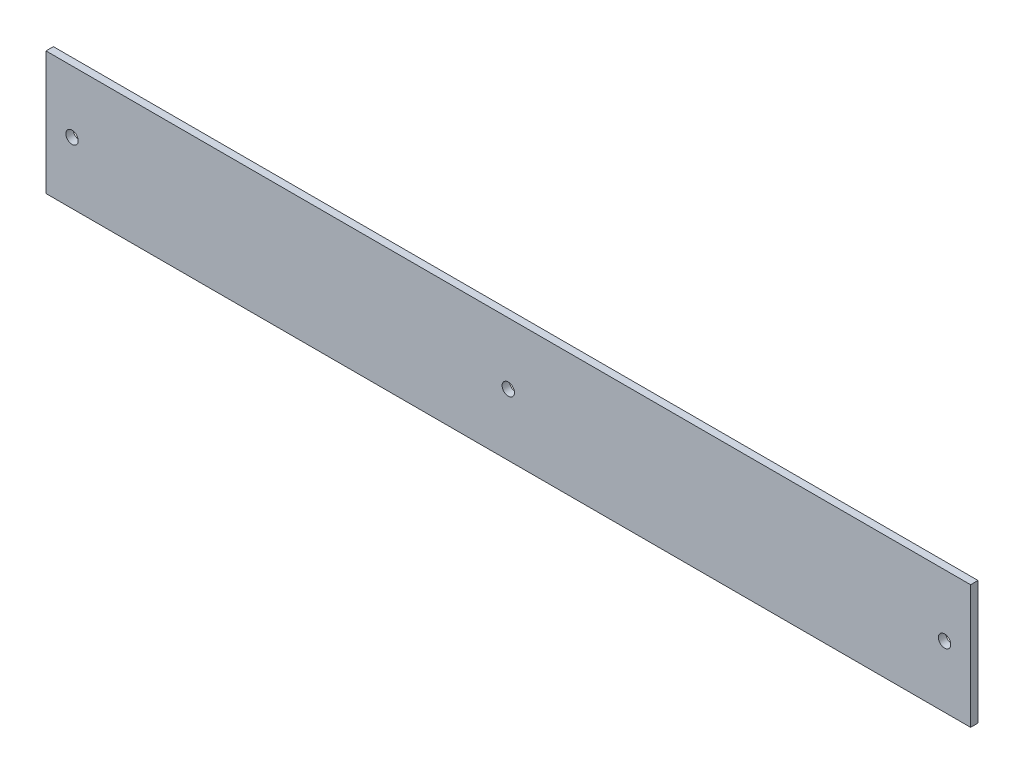
SolidWorks part; units mm, degrees
material "6061 Alloy"
ref_plane "Front Plane" through (0, 0, 0) normal (0, 0, 1) x (1, 0, 0)
ref_plane "Top Plane" through (0, 0, 0) normal (0, 1, 0) x (1, 0, 0)
ref_plane "Right Plane" through (0, 0, 0) normal (1, 0, 0) x (0, 0, -1)
sketch "Sketch1" plane through (0, 0, 0) normal (0, 0, 1) x (1, 0, 0)
  line L0 (0, 25.4) -> (380.1872, 25.4) construction
  line L1 (0, 0) -> (380.1872, 0)
  line L2 (0, 0) -> (0, 50.8)
  line L3 (0, 50.8) -> (380.1872, 50.8)
  line L4 (380.1872, 0) -> (380.1872, 50.8)
  line L5 (-1.9939, 50.8) -> (-1.9939, 0) construction
  line L6 (382.1811, 50.8) -> (382.1811, 0) construction
  line L7 (-1.9939, 32.1632) -> (0, 32.1632) construction
  line L8 (382.1811, 12.4504) -> (380.1872, 12.4504) construction
  circle A0 centre (10.7061, 25.4) radius 2.54
  circle A1 centre (190.0936, 25.4) radius 2.54
  circle A2 centre (369.4811, 25.4) radius 2.54
  dimension "D6" = 5.08
  dimension "D1" = 380.1872
  dimension "D2" = 50.8
  dimension "D3" = 12.7
  dimension "D4" = 384.175
  dimension "D5" = 12.7
extrude "Boss-Extrude1" add sketch "Sketch1" along normal blind 3.048
equation "\"base length\" = 21"
equation "\"base width\" = 16.5"
equation "\"glass pane length\" = 14.125"
equation "\"glass pane width\" = 10.1875"
equation "\"glass pane wall width\" = 3/4"
equation "\"glass lip\" = 1/4"
equation "\"bolt diameter\" = 0.2"
equation "\"stepper body width\" = 2.22"
equation "\"stepper mount offset\" = 0.19"
equation "\"stepper mount diameter\" = 0.19"
equation "\"stepper shaft offset from body\" = 0.79"
equation "\"stepper spacer thickness\" = 0.2"
equation "\"y axis stepper wall height off base\" = 8"
equation "\"y axis stepper wall bracket thickness\" = 1"
equation "\"y axis stepper wall mount side offset\" = 1/2"
equation "\"y axis stepper wall mount top offset\" = 1/2"
equation "\"y axis stepper wall width\" = \"stepper body width\" + 1                  "
equation "\"thin metal\" = 0.12"
equation "\"thick metal\" = 0.25"
equation "\"recognizer width\" = 2.5"
equation "\"recognizer nut plate height\" = 1.25"
equation "\"recognizer nut plate offset\" = 1.5"
equation "\"recognizer arm height to hole\"= 4.255"
equation "\"recognizer bracket length\" = 4"
equation "\"x axis threaded rod length\" = 3"
equation "\"D1@Sketch1\"=\"base width\"-\"thin metal\"-1.782+2*\"thin metal\" +0.13"
equation "\"D1@Boss-Extrude1\" = \"thin metal\""
